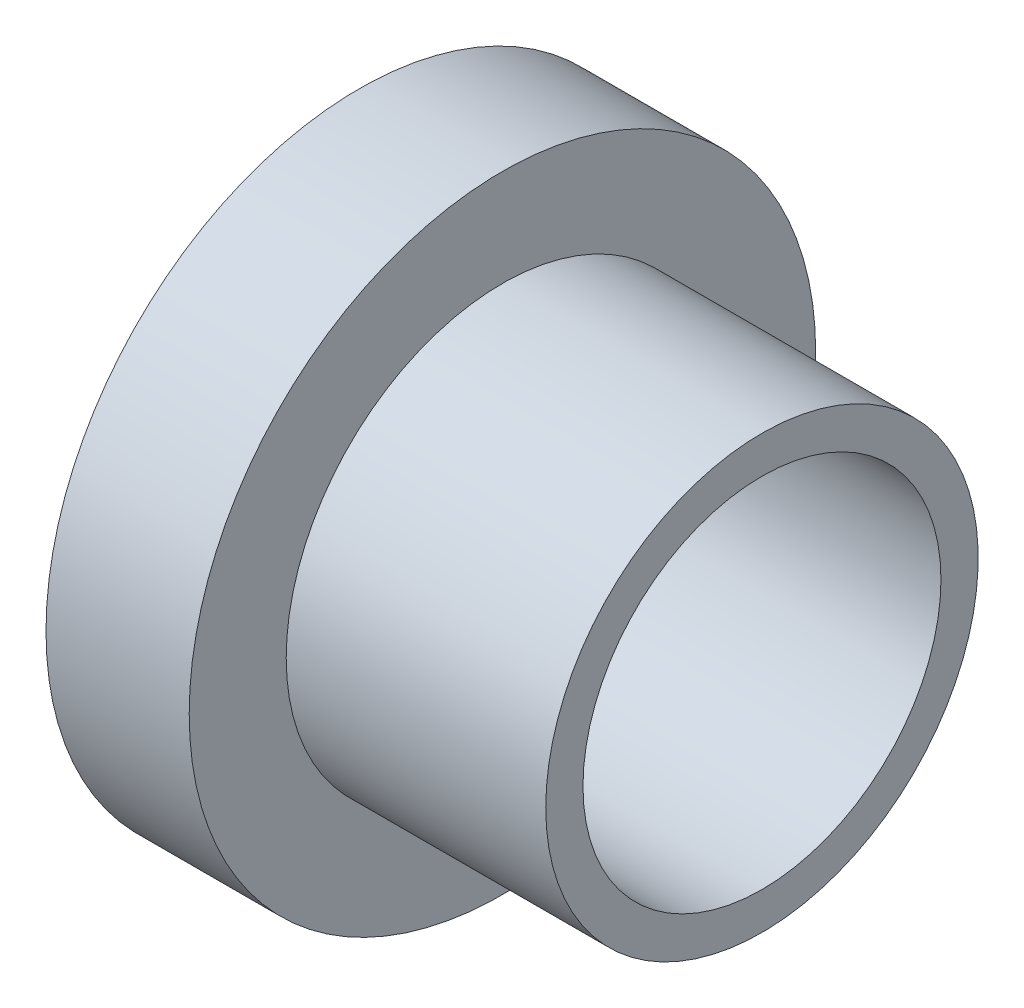
SolidWorks part; units mm, degrees
ref_plane "Plan de face" through (0, 0, 0) normal (0, 0, 1) x (1, 0, 0)
ref_plane "Plan de dessus" through (0, 0, 0) normal (0, 1, 0) x (1, 0, 0)
ref_plane "Plan de droite" through (0, 0, 0) normal (1, 0, 0) x (0, 0, -1)
sketch "Esquisse1" plane through (0, 0, 0) normal (0, 0, 1) x (1, 0, 0)
  line L0 (0, -5) -> (11.25, -5) construction
  line L2 (0, 0) -> (0, 3.75)
  line L3 (0, 3.75) -> (4, 3.75)
  line L4 (4, 1.04) -> (4, 3.75)
  line L5 (0, 0) -> (11.25, 0)
  line L7 (4, 1.04) -> (11.25, 1.04)
  line L8 (11.25, 0) -> (11.25, 1.04)
  dimension "D1" = 3.75
  dimension "D2" = 4
  dimension "D3" = 1.04
  dimension "D4" = 7.25
  dimension "D5" = 5
revolve "Révolution1" add sketch "Esquisse1" angle 360 about L0
